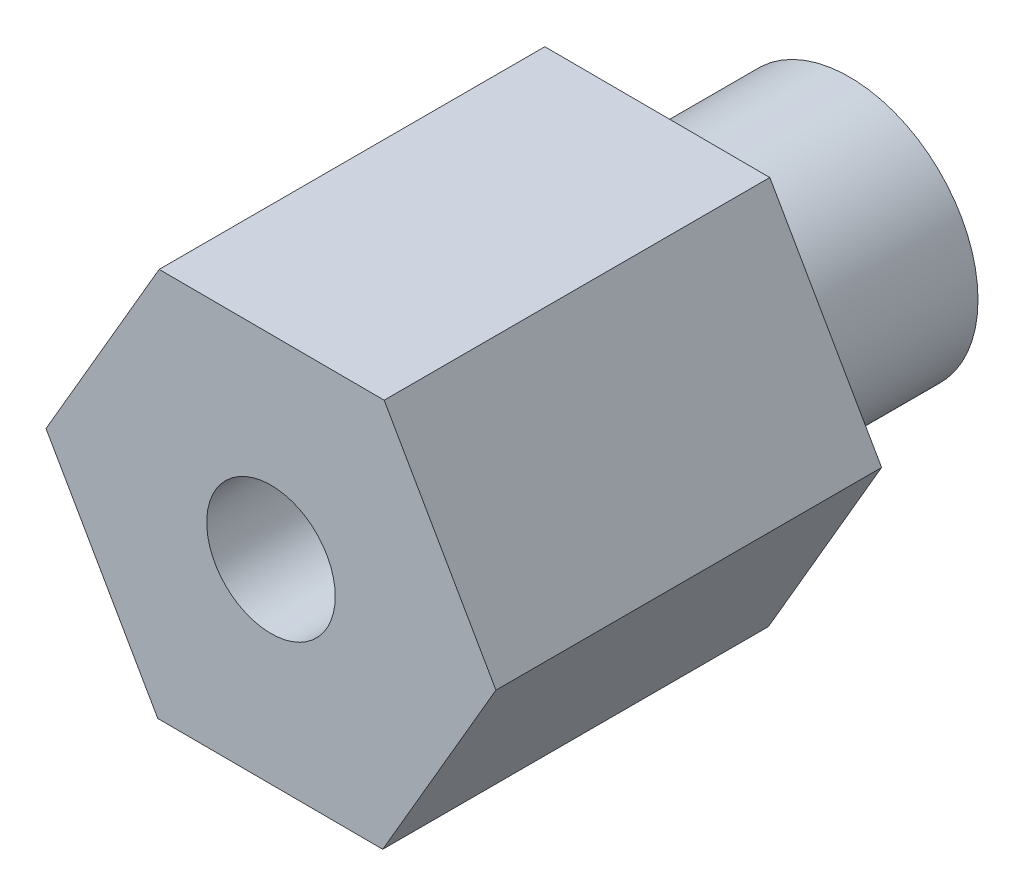
SolidWorks part; units mm, degrees
ref_plane "前视基准面" through (0, 0, 0) normal (0, 0, 1) x (1, 0, 0)
ref_plane "上视基准面" through (0, 0, 0) normal (0, 1, 0) x (1, 0, 0)
ref_plane "右视基准面" through (0, 0, 0) normal (1, 0, 0) x (0, 0, -1)
sketch "草图1" plane through (0, 0, 0) normal (0, 0, 1) x (1, 0, 0)
  circle A0 centre (0, 0) radius 2
extrude "凸台-拉伸1" add sketch "草图1" along normal blind 3
sketch "草图2" plane through (0, 0, 3) normal (0, 0, 1) x (1, 0, 0)
  line L1 (1.7609, 3.0248) -> (-1.7391, 3.0374)
  line L2 (-1.7391, 3.0374) -> (-3.5, 0.0126)
  line L3 (-3.5, 0.0126) -> (-1.7609, -3.0248)
  line L4 (-1.7609, -3.0248) -> (1.7391, -3.0374)
  line L5 (1.7391, -3.0374) -> (3.5, -0.0126)
  line L6 (3.5, -0.0126) -> (1.7609, 3.0248)
  circle A0 centre (0, 0) radius 3.5 construction
extrude "凸台-拉伸2" add sketch "草图2" along normal blind 6
sketch "草图3" plane through (0, 0, 9) normal (0, 0, 1) x (1, 0, 0)
  circle A0 centre (0, 0) radius 1
extrude "切除-拉伸1" cut sketch "草图3" against normal blind 10
